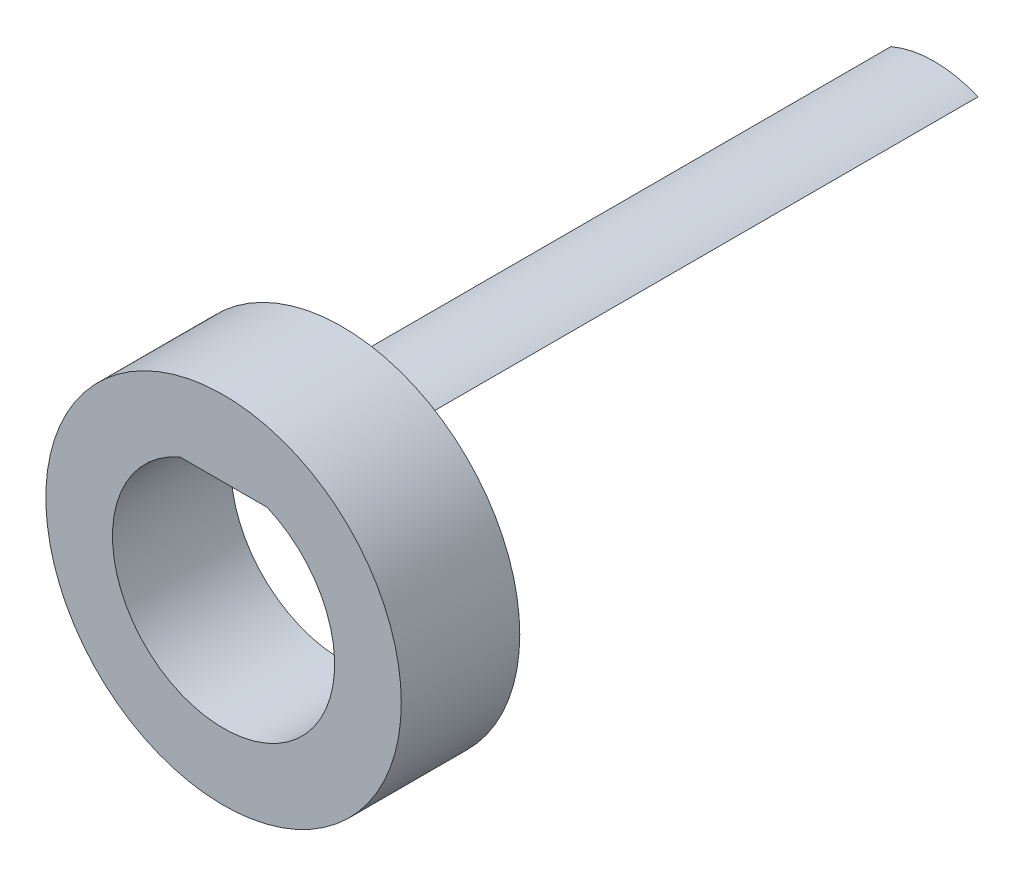
SolidWorks part; units mm, degrees
ref_plane "Front Plane" through (0, 0, 0) normal (0, 0, 1) x (1, 0, 0)
ref_plane "Top Plane" through (0, 0, 0) normal (0, 1, 0) x (1, 0, 0)
ref_plane "Right Plane" through (0, 0, 0) normal (1, 0, 0) x (0, 0, -1)
sketch "Sketch1" plane through (0, 0, 0) normal (0, 0, 1) x (1, 0, 0)
  line L0 (-0.9333, 2.1907) -> (0.9333, 2.1907)
  line L1 (-6.7495, -2.3812) -> (6.7495, -2.3812) construction
  arc A0 (-0.9333, 2.1907) -> (0.9333, 2.1907) centre (0, 0) ccw
  circle A1 centre (0, 0) radius 3.81
  point P7 (0, -2.3812)
  point P8 (0, -2.3812)
  dimension "D1" = 4.7625
  dimension "D2" = 7.62
  dimension "D3" = 4.572
extrude "Boss-Extrude1" add sketch "Sketch1" along normal blind 2.54
sketch "Sketch2" plane through (0, 0, 0) normal (0, 0, -1) x (-1, 0, 0)
  line L0 (-0.9333, 2.1907) -> (0.9333, 2.1907)
  arc A0 (0.9333, 2.1907) -> (-0.9333, 2.1907) centre (0, 0) ccw
extrude "Boss-Extrude2" add sketch "Sketch2" along normal blind 12.7
